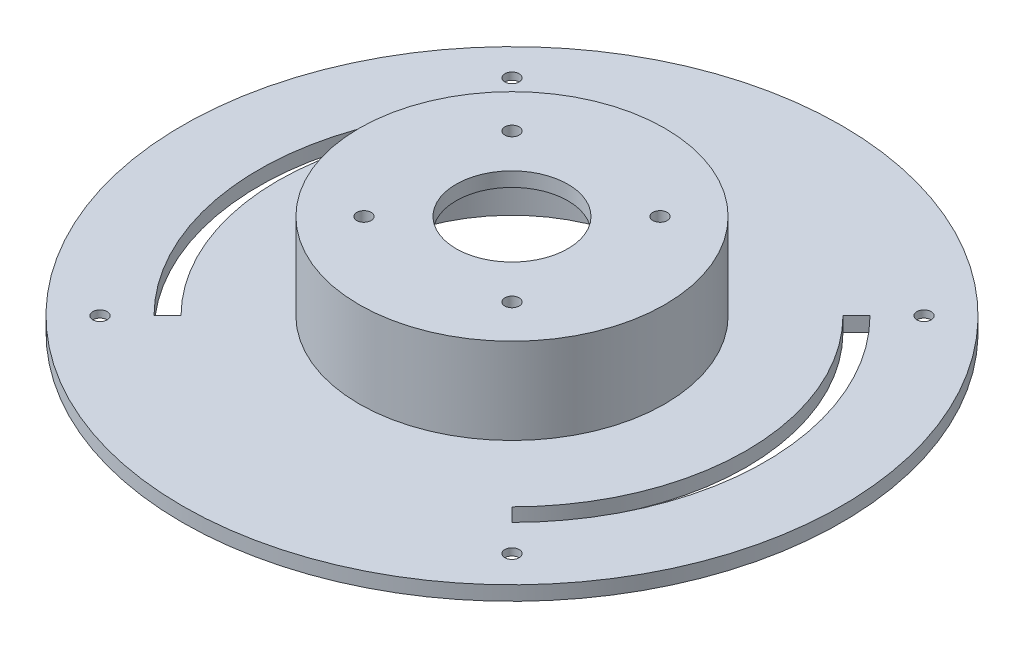
SolidWorks part; units mm, degrees
ref_plane "Front Plane" through (0, 0, 0) normal (0, 0, 1) x (1, 0, 0)
ref_plane "Top Plane" through (0, 0, 0) normal (0, 1, 0) x (1, 0, 0)
ref_plane "Right Plane" through (0, 0, 0) normal (1, 0, 0) x (0, 0, -1)
sketch "Sketch1" plane through (0, 0, 0) normal (0, 1, 0) x (1, 0, 0)
  circle A0 centre (0, 0) radius 69
  dimension "D1" = 138
extrude "Boss-Extrude1" add sketch "Sketch1" along normal blind 3
sketch "Sketch2" plane through (0, 3, 0) normal (0, 1, 0) x (1, 0, 0)
  circle A0 centre (0, 0) radius 32
  dimension "D1" = 64
extrude "Boss-Extrude2" add sketch "Sketch2" along normal blind 18
sketch "Sketch3" plane through (0, 21, 0) normal (0, 1, 0) x (1, 0, 0)
  line L0 (0, 56.364) -> (0, -54.6297) construction
  line L1 (-45.6693, 0) -> (37.576, 0) construction
  circle A0 centre (0, 0) radius 11.7
  circle A1 centre (15.5, 15.5) radius 1.5
  circle A2 centre (-15.5, 15.5) radius 1.5
  circle A3 centre (15.5, -15.5) radius 1.5
  circle A4 centre (-15.5, -15.5) radius 1.5
  dimension "D1" = 23.4
  dimension "D2" = 3
  dimension "D3" = 15.5
  dimension "D4" = 15.5
extrude "Cut-Extrude1" cut sketch "Sketch3" against normal through all
ref_plane "Plane2" through (0, 0, 0) normal (0, -1, 0) x (-1, 0, 0)
sketch "Sketch6" plane through (0, 0, 0) normal (0, -1, 0) x (-1, 0, 0)
  circle A0 centre (0, 0) radius 30
  dimension "D1" = 60
extrude "Cut-Extrude3" cut sketch "Sketch6" against normal blind 18
sketch "Sketch7" plane through (0, 3, 0) normal (0, 1, 0) x (1, 0, 0)
  line L0 (0, 73.7068) -> (0, -77.7534) construction
  line L1 (-89.2189, 0) -> (93.0728, 0) construction
  line L2 (0, 0) -> (55.0633, 55.0633) construction
  line L3 (0, 0) -> (-61.1332, 61.1332) construction
  line L4 (0, 0) -> (-63.9579, -63.9579) construction
  line L5 (0, 0) -> (64.7945, -64.7945) construction
  line L6 (34.6482, 34.6482) -> (37.4767, 37.4767)
  line L7 (37.4767, -37.4767) -> (34.6482, -34.6482)
  line L8 (-37.4767, -37.4767) -> (-34.6482, -34.6482)
  line L9 (-34.6482, 34.6482) -> (-37.4767, 37.4767)
  arc A0 (34.6482, 34.6482) -> (34.6482, -34.6482) centre (0, 0) cw
  circle A1 centre (0, 0) radius 69 construction
  arc A2 (37.4767, 37.4767) -> (37.4767, -37.4767) centre (0, 0) cw
  arc A3 (-34.6482, 34.6482) -> (-34.6482, -34.6482) centre (0, 0) ccw
  arc A4 (-37.4767, 37.4767) -> (-37.4767, -37.4767) centre (0, 0) ccw
  circle A5 centre (43.1335, 43.1335) radius 1.5
  circle A6 centre (43.1335, -43.1335) radius 1.5
  circle A7 centre (-43.1335, -43.1335) radius 1.5
  circle A8 centre (-43.1335, 43.1335) radius 1.5
  dimension "D5" = 20
  dimension "D7" = 12
  dimension "D8" = 3
  dimension "D1" = 45
  dimension "D2" = 45
  dimension "D3" = 45
  dimension "D4" = 45
  dimension "D6" = 4
extrude "Cut-Extrude5" cut sketch "Sketch7" against normal through all
sketch "Sketch8" plane through (0, 0, 0) normal (0, -1, 0) x (1, 0, 0)
  line L0 (0, 119.0407) -> (0, -90.7373) construction
  line L1 (-103.8901, 0) -> (87.907, 0) construction
  circle A0 centre (-43.1335, 43.1335) radius 4.05
  circle A1 centre (43.1335, 43.1335) radius 4.05
  circle A2 centre (43.1335, -43.1335) radius 4.05
  circle A3 centre (-43.1335, -43.1335) radius 4.05
  dimension "D1" = 8.1
extrude "Cut-Extrude6" cut sketch "Sketch8" against normal blind 1.5
